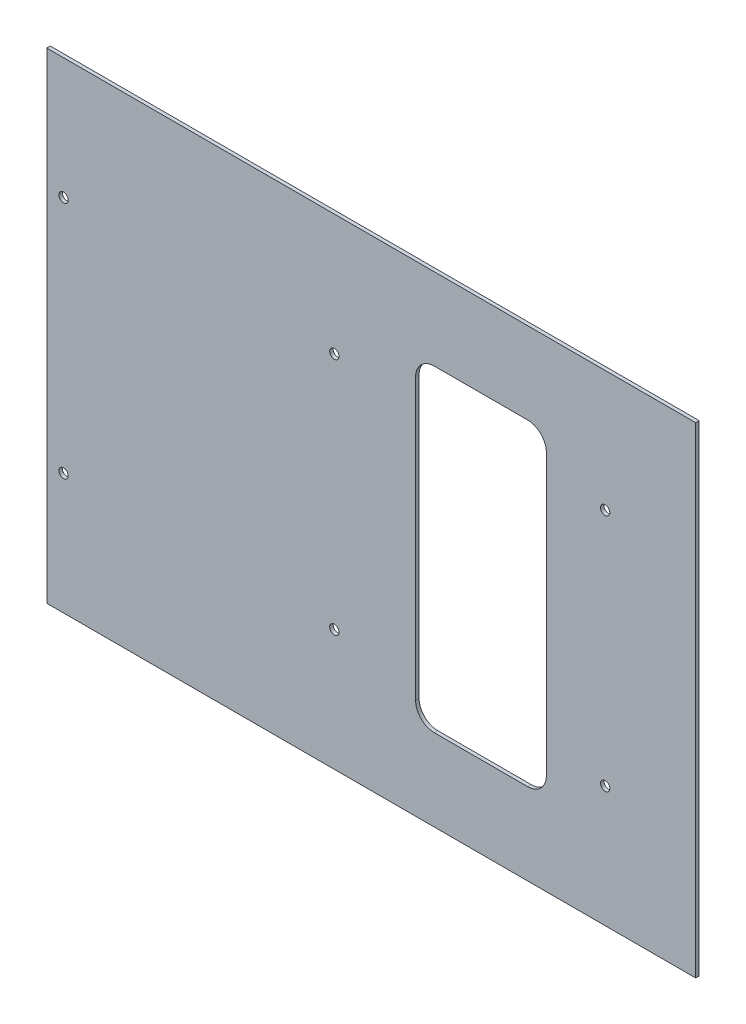
SolidWorks part; units mm, degrees
material "Perspex (TM) GS Acrylic Cast Sheet"
ref_plane "Front Plane" through (0, 0, 0) normal (0, 0, 1) x (1, 0, 0)
ref_plane "Top Plane" through (0, 0, 0) normal (0, 1, 0) x (1, 0, 0)
ref_plane "Right Plane" through (0, 0, 0) normal (1, 0, 0) x (0, 0, -1)
sketch "Sketch1" plane through (0, 0, 0) normal (0, 0, 1) x (1, 0, 0)
  line L0 (-1276.35, 426.5625) -> (-1276.35, 421.8) construction
  line L1 (-393.7, -235.425) -> (-1276.35, -235.425)
  line L2 (-393.7, -235.425) -> (-393.7, 418.625)
  line L3 (-393.7, 418.625) -> (-1276.35, 418.625)
  line L4 (-1276.35, -235.425) -> (-1276.35, 418.625)
  line L5 (-1276.35, 421.8) -> (-393.7, 421.8) construction
  line L6 (-406.1223, 91.6) -> (-393.7, 91.6) construction
  line L7 (-406.1223, 429.65) -> (-406.1223, -246.45) construction
  line L8 (-393.7, 426.5625) -> (-393.7, 421.8) construction
  dimension "D1" = 3.175
extrude "Extrude1" add sketch "Sketch1" along normal blind 4.7625
sketch "Sketch2" plane through (0, 0, 0) normal (0, 0, -1) x (-1, 0, 0)
  circle A0 centre (516.89, 254) radius 6.35
  circle A1 centre (516.89, -70.8) radius 6.35
  circle A2 centre (885.19, 254) radius 6.35
  circle A3 centre (885.19, -70.8) radius 6.35
  circle A4 centre (1253.49, -70.8) radius 6.35
  circle A5 centre (1253.49, 254) radius 6.35
  dimension "D1" = 12.7
  dimension "D2" = 12.7
extrude "Cut-Extrude1" cut sketch "Sketch2" against normal through all
sketch "Sketch3" plane through (0, 0, 4.7625) normal (0, 0, 1) x (1, 0, 0)
  line L0 (-596.9, 91.6) -> (-393.7, 91.6) construction
  line L1 (-596.9, 307.5) -> (-774.7, 307.5)
  line L2 (-596.9, 307.5) -> (-596.9, -124.3)
  line L3 (-596.9, -124.3) -> (-774.7, -124.3)
  line L4 (-774.7, 307.5) -> (-774.7, -124.3)
  line L5 (-393.7, -235.425) -> (-393.7, 418.625) construction
  dimension "D1" = 177.8
  dimension "D2" = 431.8
  dimension "D3" = 203.2
extrude "Cut-Extrude2" cut sketch "Sketch3" against normal through all
fillet "Fillet1" radius 25.4 4 edges at (-774.7, -124.3, 2.3813) (-596.9, -124.3, 2.3813) (-774.7, 307.5, 2.3813) (-596.9, 307.5, 2.3813)
